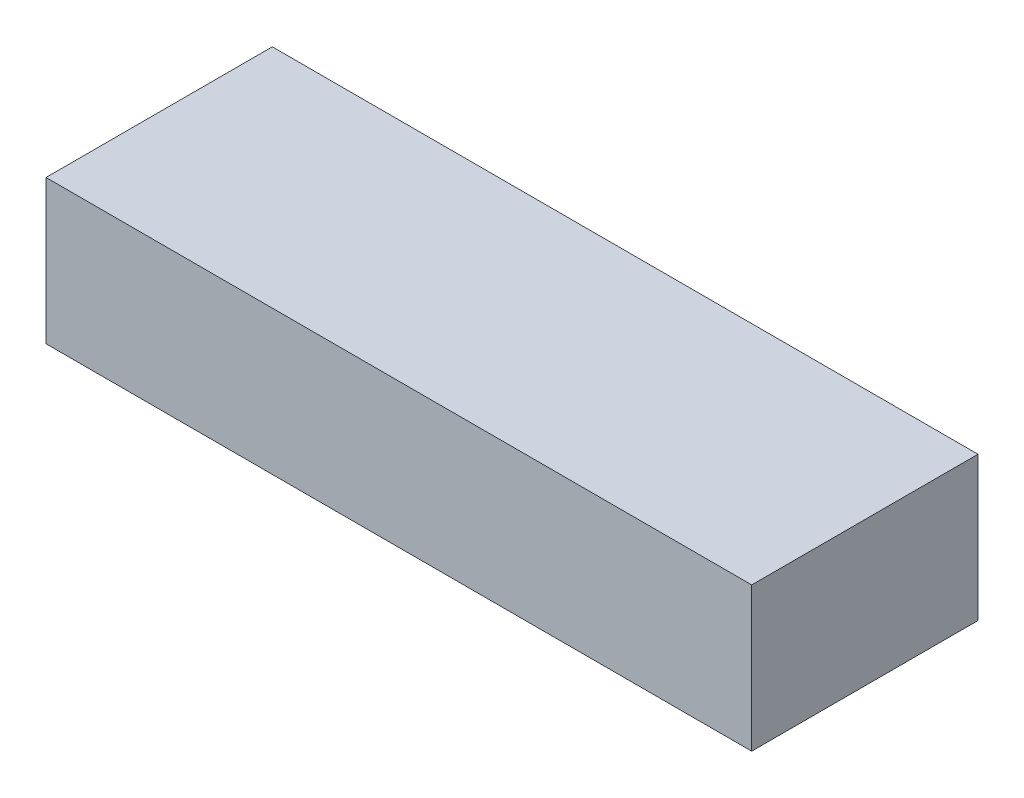
SolidWorks part; units mm, degrees
material "Thermal-Paste"
ref_plane "Ön Düzlem" through (0, 0, 0) normal (0, 0, 1) x (1, 0, 0)
ref_plane "Üst Düzlem" through (0, 0, 0) normal (0, 1, 0) x (1, 0, 0)
ref_plane "Sağ Düzlem" through (0, 0, 0) normal (1, 0, 0) x (0, 0, -1)
sketch "Sketch1" plane through (0, 0, 0) normal (0, 1, 0) x (1, 0, 0)
  line L1 (-43.2091, 15.7136) -> (5.7909, 15.7136)
  line L2 (-43.2091, 15.7136) -> (-43.2091, 0)
  line L3 (-43.2091, 0) -> (5.7909, 0)
  line L4 (5.7909, 15.7136) -> (5.7909, 0)
  dimension "D1" = 49
  dimension "D2" = 15.7136
extrude "Boss-Extrude2" add sketch "Sketch1" along normal blind 10
